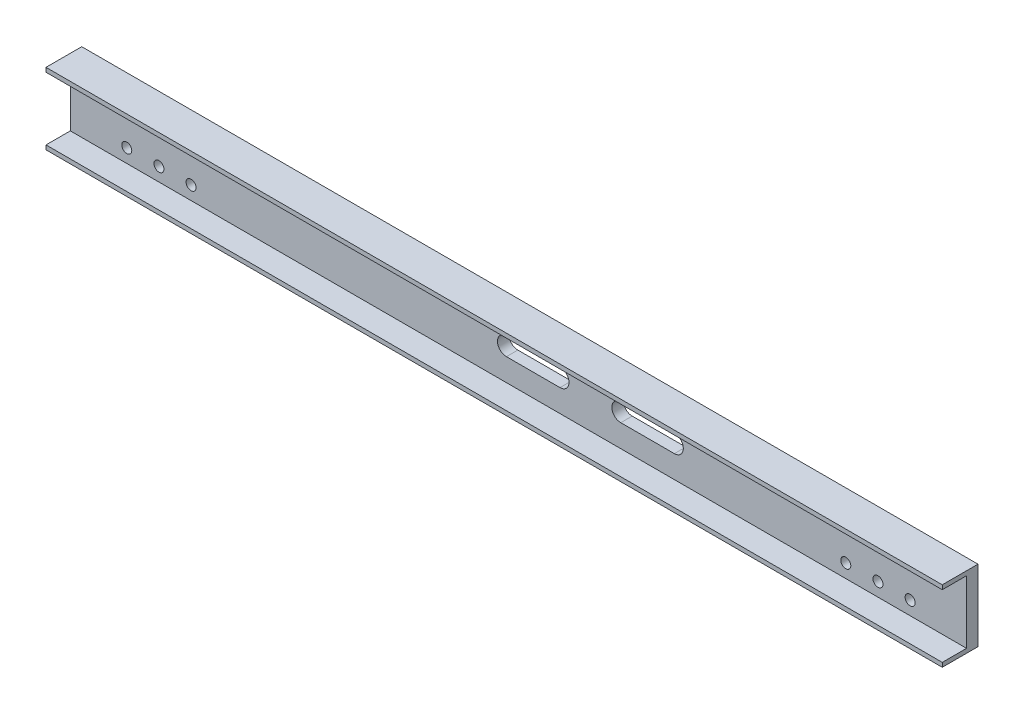
SolidWorks part; units mm, degrees
ref_plane "Front Plane" through (0, 0, 0) normal (0, 0, 1) x (1, 0, 0)
ref_plane "Top Plane" through (0, 0, 0) normal (0, 1, 0) x (1, 0, 0)
ref_plane "Right Plane" through (0, 0, 0) normal (1, 0, 0) x (0, 0, -1)
sketch "Sketch1" plane through (0, 0, 0) normal (1, 0, 0) x (0, 0, -1)
  line L1 (-8, -50) -> (8, -50)
  line L2 (-8, -50) -> (-8, 50)
  line L3 (-8, 50) -> (8, 50)
  line L4 (8, -50) -> (8, 50)
  line L5 (-8, -50) -> (8, 50) construction
  line L6 (-8, 50) -> (8, -50) construction
  line L7 (8, 50) -> (-42, 50)
  line L8 (8, 50) -> (8, 44)
  line L9 (8, 44) -> (-42, 44)
  line L10 (-42, 50) -> (-42, 44)
  line L11 (8, -50) -> (-42, -50)
  line L12 (8, -50) -> (8, -44)
  line L13 (8, -44) -> (-42, -44)
  line L14 (-42, -50) -> (-42, -44)
  point P0 (0, 0)
  dimension "D1" = 100
  dimension "D2" = 50
  dimension "D3" = 50
  dimension "D4" = 6
  dimension "D5" = 6
  dimension "D6" = 16
extrude "Boss-Extrude1" add sketch "Sketch1" along normal blind 1254 contours L7 L10 L9 L2 | L9 L4 L3 L2 | L13 L4 L9 L2 | L4 L13 L2 L1 | L14 L11 L2 L13
hole_wizard "Ø12.0mm Dowel Hole1" positions "Sketch4" profile "Sketch6" hole size "Ø12.0" standard "ISO" end condition through all
sketch "Sketch4" plane through (0, 0, 8) normal (0, 0, 1) x (1, 0, 0)
  line L0 (1254, -44) -> (1254, 44) construction
  line L1 (1254, -44) -> (0, -44) construction
  line L2 (0, -44) -> (0, 44) construction
  point P4 (1175, 25)
  point P6 (1130, 25)
  point P8 (1085, 25)
  point P10 (1085, -25)
  point P12 (1130, -25)
  point P14 (1175, -25)
  point P16 (79, 25)
  point P18 (124, 25)
  point P20 (169, 25)
  point P22 (169, -25)
  point P24 (124, -25)
  point P26 (79, -25)
  point P29 (0, 0)
  point P30 (0, 0)
  point P31 (0, 0)
  point P32 (0, 0)
  point P33 (0, 0)
  point P34 (0, 0)
  point P35 (0, 0)
  point P38 (1102.3031, 23.9251)
  dimension "D1" = 79
  dimension "D2" = 45
  dimension "D3" = 45
  dimension "D4" = 50
  dimension "D5" = 19
  dimension "D6" = 45
  dimension "D7" = 45
  dimension "D8" = 79
sketch "Sketch6" plane through (1175, 25, 8) normal (1, 0, 0) x (0, -1, 0)
  line L0 (0, 0) -> (0, 16)
  line L1 (0, 16) -> (7, 16)
  line L2 (7, 16) -> (7, 0)
  line L5 (7, 0) -> (0, 0)
  line L11 (0, -6.35) -> (0, 107.95) construction
  dimension "Thru Hole Dia." = 14
  dimension "Thru Hole Depth" = 16
sketch "Sketch7" plane through (0, 0, 8) normal (0, 0, 1) x (1, 0, 0)
  line L0 (770.18, 0) -> (845.18, 0) construction
  line L1 (770.18, 12.5) -> (845.18, 12.5)
  line L2 (770.18, -12.5) -> (845.18, -12.5)
  line L3 (685.18, 0) -> (610.18, 0) construction
  line L4 (685.18, -12.5) -> (610.18, -12.5)
  line L5 (685.18, 12.5) -> (610.18, 12.5)
  line L6 (1254, -44) -> (1254, 44) construction
  arc A0 (770.18, 12.5) -> (770.18, -12.5) centre (770.18, 0) ccw
  arc A1 (845.18, -12.5) -> (845.18, 12.5) centre (845.18, 0) ccw
  arc A2 (685.18, -12.5) -> (685.18, 12.5) centre (685.18, 0) ccw
  arc A3 (610.18, 12.5) -> (610.18, -12.5) centre (610.18, 0) ccw
  point P2 (807.68, 0)
  point P9 (647.68, 0)
  point P15 (646.246, 0)
  point P16 (0, 0)
  dimension "D1" = 75
  dimension "D2" = 25
  dimension "D3" = 235
  dimension "D4" = 446.32
extrude "Cut-Extrude1" cut sketch "Sketch7" against normal through all both and the other way through all
